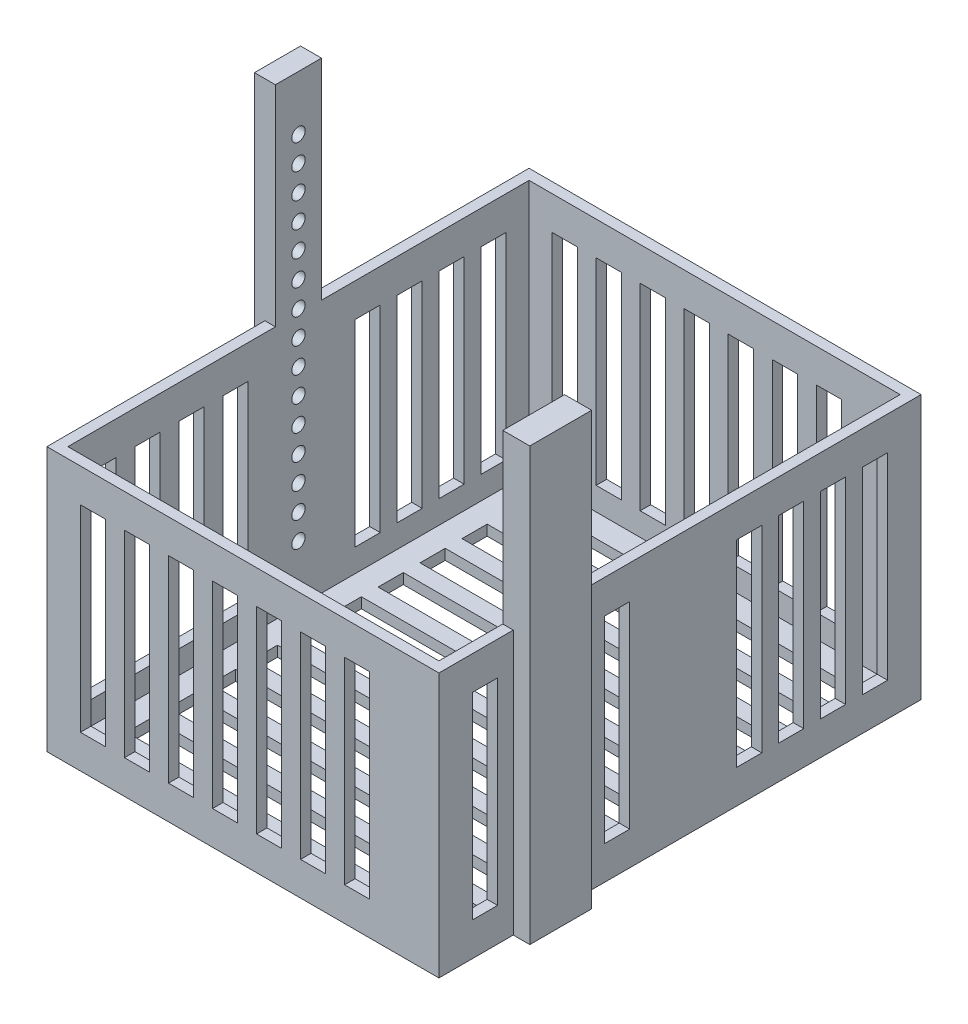
SolidWorks part; units mm, degrees
ref_plane "Front Plane" through (0, 0, 0) normal (0, 0, 1) x (1, 0, 0)
ref_plane "Top Plane" through (0, 0, 0) normal (0, 1, 0) x (1, 0, 0)
ref_plane "Right Plane" through (0, 0, 0) normal (1, 0, 0) x (0, 0, -1)
sketch "Sketch1" plane through (0, 0, 0) normal (0, 1, 0) x (1, 0, 0)
  line L1 (-46.75, 57.5) -> (46.75, 57.5)
  line L2 (-46.75, 57.5) -> (-46.75, -57.5)
  line L3 (-46.75, -57.5) -> (46.75, -57.5)
  line L4 (46.75, 57.5) -> (46.75, -57.5)
  point P4 (0, 57.5)
  point P6 (-46.75, 0)
  dimension "D1" = 93.5
  dimension "D2" = 115
extrude "Boss-Extrude1" add sketch "Sketch1" against normal blind 2.5
sketch "Sketch2" plane through (0, 0, 0) normal (0, 1, 0) x (1, 0, 0)
  line L1 (-46.75, 57.5) -> (46.75, 57.5)
  line L2 (-46.75, 57.5) -> (-46.75, -57.5)
  line L3 (-46.75, -57.5) -> (46.75, -57.5)
  line L4 (46.75, 57.5) -> (46.75, -57.5)
  line L5 (44.25, -55) -> (-44.25, -55)
  line L6 (44.25, -55) -> (44.25, 55)
  line L7 (44.25, 55) -> (-44.25, 55)
  line L8 (-44.25, -55) -> (-44.25, 55)
  dimension "D1" = 2.5
  dimension "D2" = 2.5
  dimension "D3" = 2.5
  dimension "D4" = 2.5
extrude "Boss-Extrude2" add sketch "Sketch2" along normal blind 60.5
sketch "Sketch3" plane through (0, -2.5, 0) normal (0, -1, 0) x (1, 0, 0)
  line L0 (-44.25, -55) -> (-44.25, 55) construction
  line L1 (-44.25, -5.5) -> (-49.25, -5.5)
  line L2 (-44.25, -5.5) -> (-44.25, 5.5)
  line L3 (-44.25, 5.5) -> (-49.25, 5.5)
  line L4 (-49.25, -5.5) -> (-49.25, 5.5)
  point P6 (-44.25, 0)
  dimension "D1" = 11
  dimension "D2" = 5
extrude "Boss-Extrude3" add sketch "Sketch3" against normal through all
sketch "Sketch4" plane through (0, 60.5, 0) normal (0, 1, 0) x (1, 0, 0)
  line L0 (-44.25, 55) -> (-44.25, -55) construction
  line L1 (-49.25, 5.5) -> (-44.25, 5.5)
  line L2 (-49.25, 5.5) -> (-49.25, -5.5)
  line L3 (-49.25, -5.5) -> (-44.25, -5.5)
  line L4 (-44.25, 5.5) -> (-44.25, -5.5)
  line L5 (-46.75, -5.5) -> (-49.25, -5.5) construction
extrude "Boss-Extrude4" add sketch "Sketch4" along normal blind 50
sketch "Sketch5" plane through (-49.25, 0, 0) normal (-1, 0, 0) x (0, 0, 1)
  line L1 (5.5, -2.5) -> (-5.5, -2.5) construction
  circle A0 centre (0, 97.5) radius 1.6
  dimension "D1" = 3.2
  dimension "D2" = 100
extrude "Cut-Extrude1" cut sketch "Sketch5" against normal up to next (5 mm away)
pattern_linear "LPattern1" count 15 spacing 6 along (0, -1, 0) of "Cut-Extrude1"
sketch "Sketch6" plane through (0, 0, 0) normal (0, 0, 1) x (1, 0, 0)
  line L0 (-46.75, -2.5) -> (-46.75, 60.5) construction
  line L1 (-38.75, 52.5) -> (-32.75, 52.5)
  line L2 (-38.75, 52.5) -> (-38.75, 5.5)
  line L3 (-38.75, 5.5) -> (-32.75, 5.5)
  line L4 (-32.75, 52.5) -> (-32.75, 5.5)
  line L5 (-46.75, 60.5) -> (46.75, 60.5) construction
  line L6 (-46.75, -2.5) -> (46.75, -2.5) construction
  dimension "D1" = 8
  dimension "D2" = 8
  dimension "D3" = 8
  dimension "D4" = 6
extrude "Cut-Extrude2" cut sketch "Sketch6" against normal through all both and the other way through all
pattern_linear "LPattern2" count 7 spacing 10.5 along (1, 0, 0) of "Cut-Extrude2"
sketch "Sketch7" plane through (0, 0, 0) normal (1, 0, 0) x (0, 0, -1)
  line L0 (-57.5, -2.5) -> (-57.5, 60.5) construction
  line L1 (-43.5, 52.5) -> (-49.5, 52.5)
  line L2 (-43.5, 52.5) -> (-43.5, 5.5)
  line L3 (-43.5, 5.5) -> (-49.5, 5.5)
  line L4 (-49.5, 52.5) -> (-49.5, 5.5)
  line L5 (-5.5, 60.5) -> (-57.5, 60.5) construction
  line L6 (-5.5, -2.5) -> (-57.5, -2.5) construction
  dimension "D1" = 8
  dimension "D2" = 8
  dimension "D3" = 6
  dimension "D4" = 8
extrude "Cut-Extrude3" cut sketch "Sketch7" along normal through all both and the other way through all
pattern_linear "LPattern3" count 4 spacing 10.5 along (0, 0, -1) of "Cut-Extrude3"
sketch "Sketch8" plane through (0, 0, 0) normal (1, 0, 0) x (0, 0, -1)
  line L0 (57.5, 60.5) -> (5.5, 60.5) construction
  line L1 (49.5, 52.5) -> (43.5, 52.5)
  line L2 (49.5, 52.5) -> (49.5, 5.5)
  line L3 (49.5, 5.5) -> (43.5, 5.5)
  line L4 (43.5, 52.5) -> (43.5, 5.5)
  line L5 (57.5, -2.5) -> (57.5, 60.5) construction
  line L6 (57.5, -2.5) -> (5.5, -2.5) construction
  dimension "D1" = 8
  dimension "D2" = 8
  dimension "D3" = 8
  dimension "D4" = 6
sketch "Sketch9" plane through (0, 0, 0) normal (0, 1, 0) x (1, 0, 0)
  line L0 (46.75, 57.5) -> (-46.75, 57.5) construction
  line L1 (-38.75, 49.5) -> (38.75, 49.5)
  line L2 (-38.75, 49.5) -> (-38.75, 43.5)
  line L3 (-38.75, 43.5) -> (38.75, 43.5)
  line L4 (38.75, 49.5) -> (38.75, 43.5)
  line L5 (-46.75, 57.5) -> (-46.75, 5.5) construction
  line L6 (46.75, -57.5) -> (46.75, 57.5) construction
  dimension "D1" = 8
  dimension "D2" = 8
  dimension "D3" = 8
  dimension "D4" = 6
extrude "Cut-Extrude4" cut sketch "Sketch8" against normal through all both and the other way through all
pattern_linear "LPattern4" count 4 spacing 10 along (0, 0, 1) of "Cut-Extrude4"
extrude "Cut-Extrude5" cut sketch "Sketch9" against normal through all both
pattern_linear "LPattern5" count 10 spacing 10 along (0, 0, 1) of "Cut-Extrude5"
sketch "Sketch11" plane through (0, 60.5, 0) normal (0, 1, 0) x (1, 0, 0)
  line L0 (44.25, -25.0246) -> (44.25, -39.7726)
  line L1 (44.25, -55) -> (44.25, 55) construction
  line L2 (44.25, -39.7726) -> (50.6911, -39.7726)
  line L3 (50.6911, -39.7726) -> (50.6911, -25.0246)
  line L4 (50.6911, -25.0246) -> (44.25, -25.0246)
extrude "Boss-Extrude5" add sketch "Sketch11" along normal blind 40
sketch "Sketch12" plane through (0, 60.5, 0) normal (0, -1, 0) x (1, 0, 0)
  line L0 (50.6911, 39.7726) -> (46.75, 39.7726)
  line L1 (46.75, 39.7726) -> (46.75, 25.0246)
  line L2 (46.75, 25.0246) -> (50.6911, 25.0246)
  line L3 (50.6911, 25.0246) -> (50.6911, 39.7726)
extrude "Boss-Extrude6" add sketch "Sketch12" along normal through all
equation "\"wall\"=2.5"
equation "\"D1@Sketch2\"=\"wall\""
equation "\"D2@Sketch2\"=\"wall\""
equation "\"D3@Sketch2\"=\"wall\""
equation "\"D4@Sketch2\"=\"wall\""
equation "\"D1@Boss-Extrude2\"=57+6-\"wall\""
